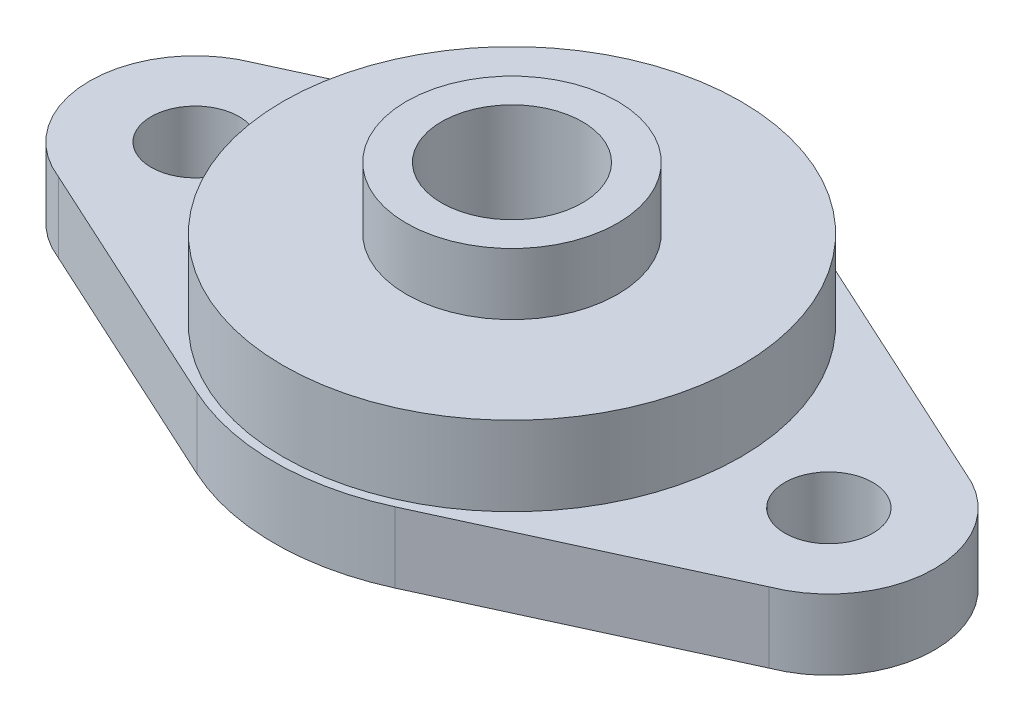
SolidWorks part; units mm, degrees
ref_plane "Front Plane" through (0, 0, 0) normal (0, 0, 1) x (1, 0, 0)
ref_plane "Top Plane" through (0, 0, 0) normal (0, 1, 0) x (1, 0, 0)
ref_plane "Right Plane" through (0, 0, 0) normal (1, 0, 0) x (0, 0, -1)
sketch "Sketch1" plane through (0, 0, 0) normal (0, 1, 0) x (1, 0, 0)
  line L0 (-20.1896, 5.5862) -> (-5.6323, 12.269)
  line L1 (20.1896, 5.5862) -> (5.6323, 12.269)
  line L2 (-20.1896, -5.5862) -> (-5.6323, -12.269)
  line L3 (20.1896, -5.5862) -> (5.6323, -12.269)
  circle A0 centre (18, 0) radius 2.5
  circle A1 centre (-18, 0) radius 2.5
  arc A2 (5.6323, 12.269) -> (-5.6323, 12.269) centre (0, 0) ccw
  arc A3 (-5.6323, -12.269) -> (5.6323, -12.269) centre (0, 0) ccw
  arc A4 (-20.1896, 5.5862) -> (-20.1896, -5.5862) centre (-18, 0) ccw
  arc A5 (20.1896, -5.5862) -> (20.1896, 5.5862) centre (18, 0) ccw
  circle A6 centre (0, 0) radius 4
extrude "Boss-Extrude1" add sketch "Sketch1" along normal blind 4
sketch "Sketch2" plane through (0, 4, 0) normal (0, 1, 0) x (1, 0, 0)
  circle A0 centre (0, 0) radius 13
  circle A1 centre (0, 0) radius 4
extrude "Boss-Extrude2" add sketch "Sketch2" along normal blind 4.5
sketch "Sketch3" plane through (0, 8.5, 0) normal (0, 1, 0) x (1, 0, 0)
  circle A0 centre (0, 0) radius 6
  circle A1 centre (0, 0) radius 4
extrude "Boss-Extrude3" add sketch "Sketch3" along normal blind 3.5
